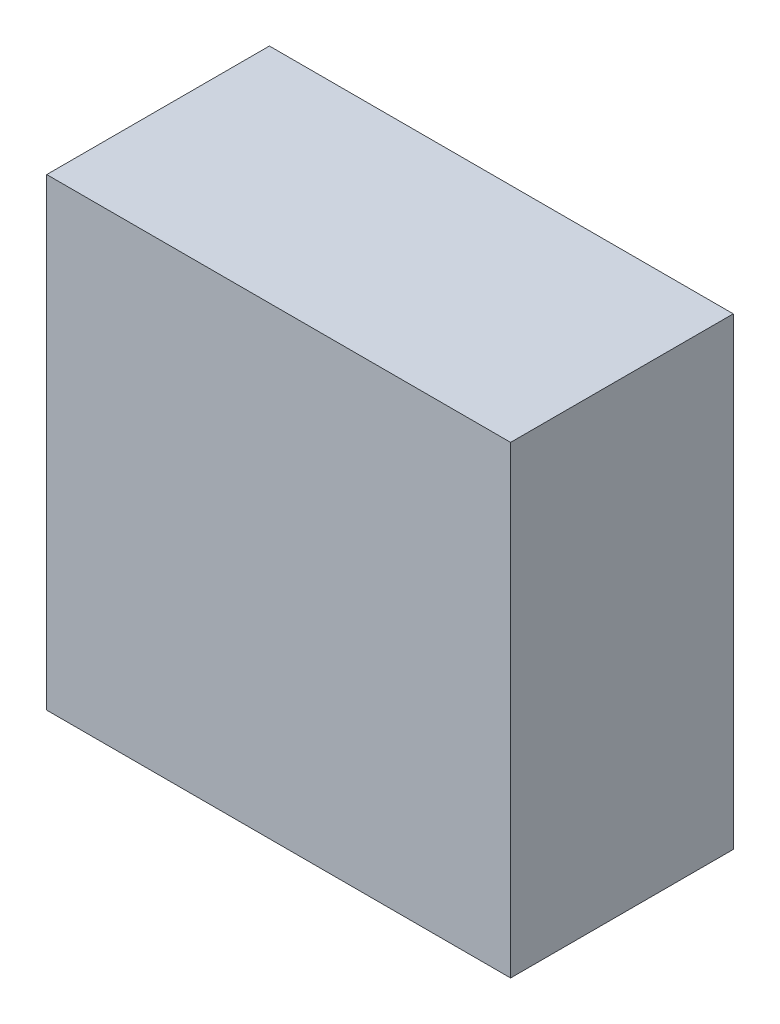
SolidWorks part; units mm, degrees
ref_plane "前视基准面" through (0, 0, 0) normal (0, 0, 1) x (1, 0, 0)
ref_plane "上视基准面" through (0, 0, 0) normal (0, 1, 0) x (1, 0, 0)
ref_plane "右视基准面" through (0, 0, 0) normal (1, 0, 0) x (0, 0, -1)
sketch "草图1" plane through (0, 0, 0) normal (0, 0, 1) x (1, 0, 0)
  line L0 (98.504, 38.6466) -> (121.3796, 38.6466) construction
  line L1 (110.4044, 48.3944) -> (110.4044, 28.072) construction
  line L2 (104.1544, 38.6466) -> (104.1544, 44.8966)
  line L3 (104.1544, 44.8966) -> (116.6544, 44.8966)
  line L4 (116.6544, 44.8966) -> (116.6544, 32.3966)
  line L5 (116.6544, 32.3966) -> (104.1544, 32.3966)
  line L6 (104.1544, 32.3966) -> (104.1544, 38.6466)
  dimension "D1" = 12.5
  dimension "D2" = 12.5
extrude "凸台-拉伸1" add sketch "草图1" along normal blind 6
